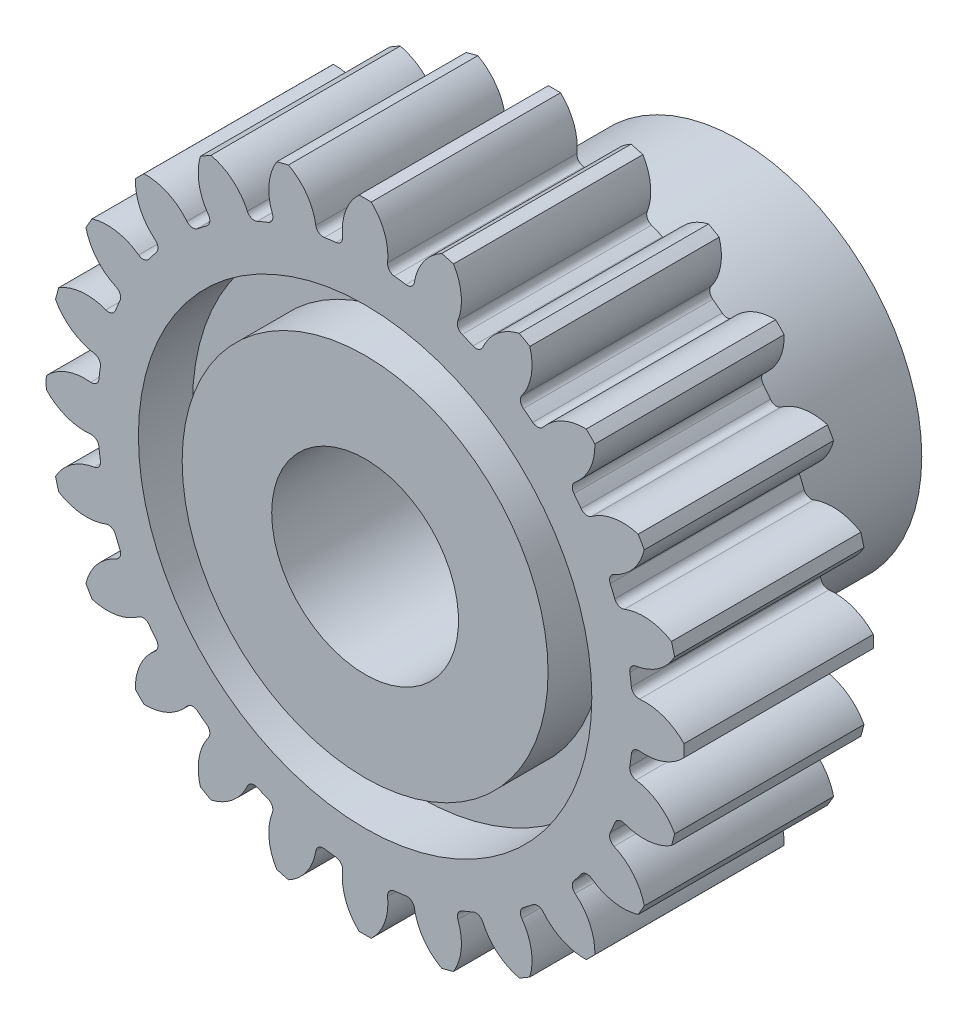
SolidWorks part; units mm, degrees
ref_plane "Front Plane" through (0, 0, 0) normal (0, 0, 1) x (1, 0, 0)
ref_plane "Top Plane" through (0, 0, 0) normal (0, 1, 0) x (1, 0, 0)
ref_plane "Right Plane" through (0, 0, 0) normal (1, 0, 0) x (0, 0, -1)
sketch "Sketch1" plane through (0, 0, 0) normal (1, 0, 0) x (0, 0, -1)
  line L0 (-9.525, 0) -> (-9.525, 16.256)
  line L1 (-9.525, 16.256) -> (0.127, 16.256)
  line L2 (0.127, 16.256) -> (0.127, 9.3269)
  line L3 (0.127, 9.3269) -> (9.525, 9.3269)
  line L4 (9.525, 9.3269) -> (9.525, 0)
  line L5 (9.525, 0) -> (-9.525, 0) construction
  line L6 (-9.525, 4.7625) -> (9.525, 4.7625)
  point P9 (-9.525, 11.557)
  dimension "OD" = 32.512
  dimension "Face Width" = 9.652
  dimension "Hub Width" = 9.398
  dimension "Hub Diameter" = 18.6538
  dimension "For Shaft Diameter" = 9.525
  dimension "Overall Width" = 19.05
  dimension "Under Cut Diameter" = 23.114
sketch "Sketch2" plane through (0, 0, 0) normal (0, 0, 1) x (1, 0, 0)
  line L0 (-1.5975, 13.5587) -> (-0.6158, 16.256)
  line L1 (-0.6158, 16.256) -> (0.6158, 16.256)
  line L2 (0.6158, 16.256) -> (1.5975, 13.5587)
  line L3 (0, 16.256) -> (0, 0) construction
  line L4 (0, 0) -> (-2.1218, 16.1169) construction
  line L5 (0, 0) -> (2.1218, 16.1169) construction
  line L6 (-5.0523, 12.6832) -> (-4.8022, 15.5427)
  line L7 (-4.8022, 15.5427) -> (-3.6126, 15.8615)
  line L8 (-3.6126, 15.8615) -> (-1.9662, 13.5102)
  line L9 (-4.2074, 15.7021) -> (0, 0) construction
  line L11 (-0.6158, 16.256) -> (0, 16.256) construction
  line L12 (-0.9975, 15.2073) -> (0.9975, 15.2073) construction
  circle A0 centre (0, 0) radius 15.24 construction
  circle A2 centre (0, 0) radius 16.256
  circle A3 centre (0, 0) radius 13.6525
  arc A5 (-0.3079, 16.256) -> (-1.0788, 13.6098) centre (1.5607, 14.2762) ccw
  arc A6 (1.0788, 13.6098) -> (0.3079, 16.256) centre (-1.5607, 14.2762) ccw
  arc A7 (-2.4804, 13.4253) -> (-3.91, 15.7818) centre (-5.2025, 13.3858) ccw
  arc A8 (-0.9975, 15.2073) -> (0.9975, 15.2073) centre (0, 0) cw
  point P3 (0, 15.24)
  point P5 (3.9444, 14.7207)
  point P6 (-13.1982, 7.62)
  point P9 (7.62, 13.1982)
  point P10 (10.7763, 10.7763)
  point P11 (13.1982, 7.62)
  point P12 (14.7207, 3.9444)
  point P13 (15.24, 0)
  point P14 (14.7207, -3.9444)
  point P15 (13.1982, -7.62)
  point P16 (10.7763, -10.7763)
  point P17 (7.62, -13.1982)
  point P18 (3.9444, -14.7207)
  point P19 (0, -15.24)
  point P20 (-3.9444, -14.7207)
  point P21 (-7.62, -13.1982)
  point P22 (-10.7763, -10.7763)
  point P23 (-13.1982, -7.62)
  point P24 (-14.7207, -3.9444)
  point P25 (-15.24, 0)
  point P26 (-14.7207, 3.9444)
  point P27 (-10.7763, 10.7763)
  point P28 (-7.62, 13.1982)
  point P29 (-3.9444, 14.7207)
  point P31 (0, 0)
  dimension "Gear Pitch Diameter" = 30.48
  dimension "Pressure Angle" = 20
  dimension "Addendum" = 1.016
  dimension "Dedendum" = 1.5875
  dimension "D1" = 15
  dimension "D2" = 1.9949
  dimension "Number of Teeth" = 24
sketch "Sketch3" plane through (0, 0, 0) normal (1, 0, 0) x (0, 0, -1)
  line L0 (-9.525, 16.256) -> (0.127, 16.256) construction
  line L1 (9.525, 9.3269) -> (9.525, 0) construction
  line L2 (0.127, 9.3269) -> (9.525, 9.3269) construction
  line L3 (0.127, 16.256) -> (0.127, 9.3269) construction
  line L4 (-9.525, 0) -> (-9.525, 16.256) construction
  line L5 (-9.525, 4.7625) -> (9.525, 4.7625) construction
  line L6 (-9.525, 16.256) -> (0.127, 16.256)
  line L7 (9.525, 9.3269) -> (9.525, 4.7625)
  line L8 (-9.525, 9.3269) -> (-6.7673, 9.3269)
  line L9 (0.127, 16.256) -> (0.127, 11.557)
  line L10 (-9.525, 4.7625) -> (-9.525, 9.3269)
  line L11 (-9.525, 4.7625) -> (9.525, 4.7625)
  line L12 (-9.525, 11.557) -> (-6.7673, 11.557)
  line L13 (-6.7673, 11.557) -> (-6.7673, 9.3269)
  line L14 (0.127, 11.557) -> (-2.6307, 11.557)
  line L15 (-2.6307, 11.557) -> (-2.6307, 9.3269)
  line L16 (-2.6307, 9.3269) -> (9.525, 9.3269)
  line L17 (-9.525, 11.557) -> (-9.525, 16.256)
  dimension "D1" = 2.7577
revolve "Revolve1" add sketch "Sketch3" angle 360 about L5
sketch "Sketch4" plane through (0, 0, 9.525) normal (0, 0, 1) x (1, 0, 0)
  arc A1 (-0.3079, 16.256) -> (-1.0788, 13.6098) centre (1.5607, 14.2762) ccw construction
  arc A2 (-2.4804, 13.4253) -> (-3.91, 15.7818) centre (-5.2025, 13.3858) ccw construction
  arc A3 (-0.311, 16.253) -> (-1.1466, 13.9904) centre (1.5607, 14.2762) ccw
  arc A4 (-2.5135, 13.8104) -> (-3.9062, 15.7797) centre (-5.2025, 13.3858) ccw
  circle A5 centre (0, 0) radius 16.256 construction
  arc A6 (-0.311, 16.253) -> (-3.9062, 15.7797) centre (0, 0) ccw
  circle A7 centre (0, 0) radius 13.6525 construction
  arc A8 (-1.4841, 13.5716) -> (-2.0791, 13.4933) centre (0, 0) ccw
  arc A9 (-2.5135, 13.8104) -> (-2.0791, 13.4933) centre (-2.1371, 13.8698) ccw
  arc A10 (-1.4841, 13.5716) -> (-1.1466, 13.9904) centre (-1.5255, 13.9503) ccw
  dimension "D1" = 0.381
extrude "Cut-Extrude1" cut sketch "Sketch4" against normal through all both and the other way through all
pattern_circular "CirPattern1" count 24 over 360 about axis through (0, 0, 0) along (0, 0, 1) of "Cut-Extrude1"
equation "\"Dedendum@Sketch2\" = 1.25 /  ( \"Number of Teeth@Sketch2\" / \"Gear Pitch Diameter@Sketch2\" ) "
equation "\"D1@Sketch2\"=360/\"Number of Teeth@Sketch2\""
equation "\"D1@Sketch4\"=.3/(\"Number of Teeth@Sketch2\"/\"Gear Pitch Diameter@Sketch2\")"
equation "\"D1@CirPattern1\"=\"Number of Teeth@Sketch2\""
equation "\"D2@Sketch2\"=1.5708/(\"Number of Teeth@Sketch2\"/\"Gear Pitch Diameter@Sketch2\")"
equation "\"D1@Sketch3\"=\"Face Width@Sketch1\"/3.5"
